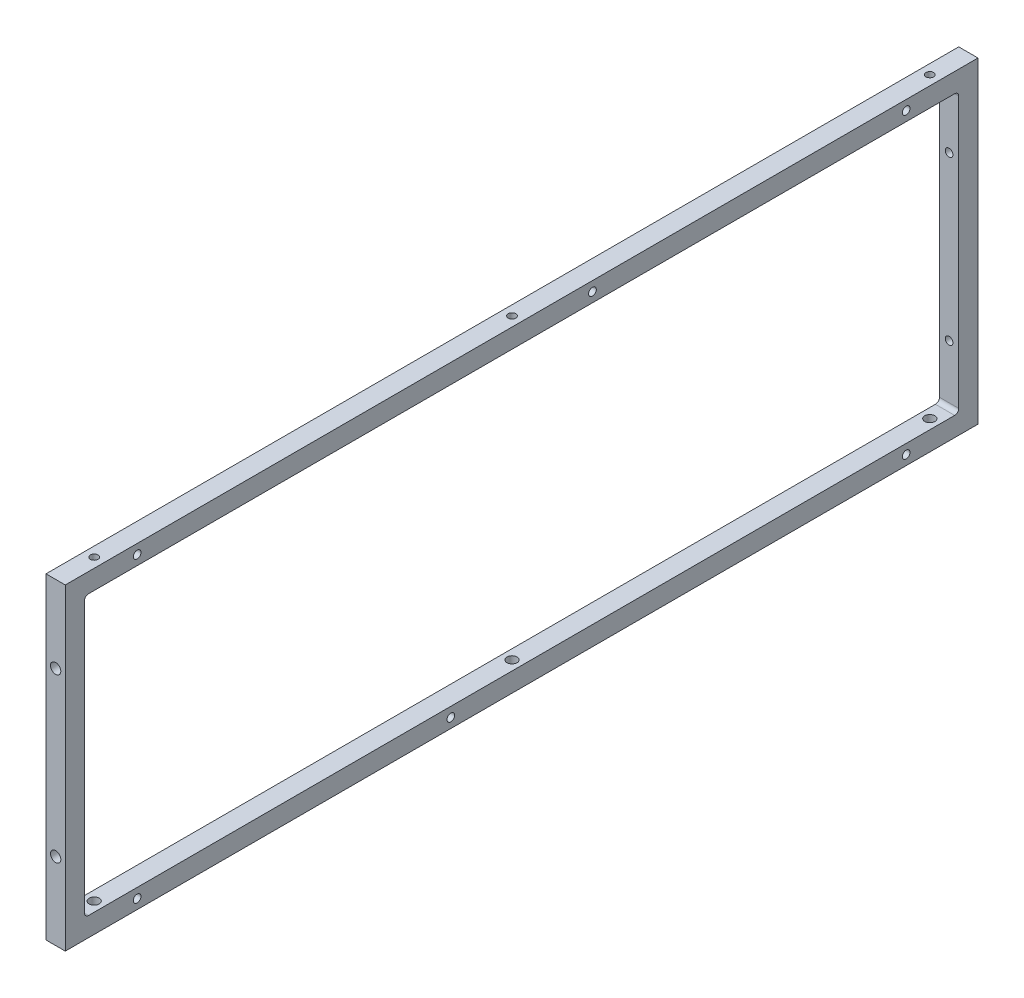
SolidWorks part; units mm, degrees
material "6061-T6 (SS)"
ref_plane "Front Plane" through (0, 0, 0) normal (0, 0, 1) x (1, 0, 0)
ref_plane "Top Plane" through (0, 0, 0) normal (0, 1, 0) x (1, 0, 0)
ref_plane "Right Plane" through (0, 0, 0) normal (1, 0, 0) x (0, 0, -1)
sketch "Sketch1" plane through (0, 0, 0) normal (1, 0, 0) x (0, 0, -1)
  line L0 (225.5, 78.3536) -> (-225.5, -78.3536) construction
  line L1 (-225.5, 78.3536) -> (225.5, 78.3536)
  line L2 (-225.5, 78.3536) -> (-225.5, -78.3536)
  line L3 (-225.5, -78.3536) -> (225.5, -78.3536)
  line L4 (225.5, 78.3536) -> (225.5, -78.3536)
  point P4 (0, 0)
  dimension "D1" = 451
  dimension "D2" = 156.7072
extrude "Extrude-Thin1" add sketch "Sketch1" along normal mid plane 9.525 thin
fillet "Fillet1" radius 2 4 edges at (0, -68.8286, -215.975) (0, -68.8286, 215.975) (0, 68.8286, 215.975) (0, 68.8286, -215.975)
hole_wizard "#10 Clearance Hole1" positions "Sketch3" profile "Sketch2" hole size "#10" standard "ANSI Inch"
sketch "Sketch3" plane through (0, -68.8286, 0) normal (0, 1, 0) x (1, 0, 0)
  line L0 (4.7625, -213.975) -> (4.7625, 213.975) construction
  line L1 (-4.7625, -213.975) -> (-4.7625, 213.975) construction
  line L3 (4.7625, 225.5) -> (-4.7625, 225.5) construction
  line L4 (4.7625, 225.5) -> (-4.7625, 225.5) construction
  line L5 (-4.7625, 0) -> (-100.6136, 0) construction
  line L6 (0, 206.45) -> (0, 397.3268) construction
  circle A0 centre (0, 206.45) radius 4.7625 construction
  point P0 (0, 206.45)
  point P2 (0, 0)
  point P26 (0, -206.45)
  dimension "D1" = 19.05
sketch "Sketch2" plane through (0, -68.8286, -206.45) normal (1, 0, 0) x (0, 0, 1)
  line L0 (0, 0) -> (0, 9.525)
  line L1 (0, 9.525) -> (2.4892, 9.525)
  line L2 (2.4892, 9.525) -> (2.4892, 0)
  line L5 (2.4892, 0) -> (0, 0)
  line L11 (0, -6.35) -> (0, 107.95) construction
  dimension "Thru Hole Dia." = 4.9784
  dimension "Thru Hole Depth" = 9.525
hole_wizard "#10-24 Tapped Hole1" positions "Sketch5" profile "Sketch4" tap size "#10-24" standard "ANSI Inch"
sketch "Sketch5" plane through (0, 0, -225.5) normal (0, 0, -1) x (-1, 0, 0)
  line L0 (0, 78.3536) -> (0, 173.2871) construction
  line L1 (-4.7625, 78.3536) -> (4.7625, 78.3536) construction
  line L2 (4.7625, 0) -> (23.2892, 0) construction
  line L3 (4.7625, -78.3536) -> (4.7625, 78.3536) construction
  point P0 (0, 40.2536)
  point P13 (0, -40.2536)
  dimension "D1" = 38.1
sketch "Sketch4" plane through (0, 40.2536, -225.5) normal (1, 0, 0) x (0, 1, 0)
  line L0 (0, 0) -> (0, 251.6008)
  line L1 (0, 251.6008) -> (1.8986, 250.46)
  line L2 (1.8986, 250.46) -> (1.8986, 0)
  line L5 (1.8986, 0) -> (0, 0)
  line L10 (0, 251.6008) -> (-1.8987, 250.46) construction
  line L11 (0, -6.35) -> (0, 107.95) construction
  dimension "Tap Drill Dia." = 3.7973
  dimension "Tap Drill Depth" = 250.46
  dimension "Drill Angle" = 118
cosmetic thread "Hole Thread1" parameters "D1"=9.525, "D2"=4.826
cosmetic thread "Hole Thread2" parameters "D1"=9.525, "D2"=4.826
hole_wizard "#10 Clearance Hole2" positions "Sketch7" profile "Sketch6" hole size "#10" standard "ANSI Inch"
sketch "Sketch7" plane through (0, 0, 225.5) normal (0, 0, 1) x (1, 0, 0)
  point P0 (0, 40.2536)
  point P3 (0, -40.2536)
sketch "Sketch6" plane through (0, 40.2536, 225.5) normal (1, 0, 0) x (0, -1, 0)
  line L0 (0, 0) -> (0, 21.5338)
  line L1 (0, 21.5338) -> (2.5527, 20)
  line L2 (2.5527, 20) -> (2.5527, 0)
  line L5 (2.5527, 0) -> (0, 0)
  line L10 (0, 21.5338) -> (-2.5527, 20) construction
  line L11 (0, -6.35) -> (0, 107.95) construction
  dimension "Hole Dia." = 5.1054
  dimension "Hole Depth" = 20
  dimension "Drill Angle" = 118
hole_wizard "#10-24 Tapped Hole2" positions "Sketch9" profile "Sketch8" tap size "#10-24" standard "ANSI Inch"
sketch "Sketch9" plane through (-4.7625, 0, 0) normal (-1, 0, 0) x (0, 0, 1)
  line L0 (0, 0) -> (0, 48.3235) construction
  line L1 (0, 0) -> (90.2804, 0) construction
  line L2 (-102.4491, 73.5911) -> (-75.598, 73.5911) construction
  line L3 (-225.5, 78.3536) -> (225.5, 78.3536) construction
  line L4 (-213.975, 68.8286) -> (213.975, 68.8286) construction
  line L5 (-151.0617, -73.5911) -> (-102.4491, -73.5911) construction
  circle A0 centre (-190, 73.5911) radius 4.7625 construction
  point P0 (-190, 73.5911)
  point P22 (-35, 73.5911)
  point P25 (-190, -73.5911)
  point P30 (35, -73.5911)
  point P33 (190, -73.5911)
  point P34 (190, 73.5911)
  dimension "D1" = 190
  dimension "D2" = 35
  dimension "D3" = 35
sketch "Sketch8" plane through (-4.7625, 73.5911, -190) normal (0, 1, 0) x (0, 0, 1)
  line L0 (0, 0) -> (0, 16.0908)
  line L1 (0, 16.0908) -> (1.8986, 14.95)
  line L2 (1.8986, 14.95) -> (1.8986, 0)
  line L5 (1.8986, 0) -> (0, 0)
  line L10 (0, 16.0908) -> (-1.8987, 14.95) construction
  line L11 (0, -6.35) -> (0, 107.95) construction
  dimension "Tap Drill Dia." = 3.7973
  dimension "Tap Drill Depth" = 14.95
  dimension "Drill Angle" = 118
cosmetic thread "Hole Thread4" parameters "D1"=9.525, "D2"=4.826
cosmetic thread "Hole Thread5" parameters "D1"=9.525, "D2"=4.826
cosmetic thread "Hole Thread6" parameters "D1"=9.525, "D2"=4.826
cosmetic thread "Hole Thread7" parameters "D1"=9.525, "D2"=4.826
cosmetic thread "Hole Thread8" parameters "D1"=9.525, "D2"=4.826
cosmetic thread "Hole Thread9" parameters "D1"=9.525, "D2"=4.826
hole_wizard "#10-24 Tapped Hole3" positions "Sketch11" profile "Sketch10" tap size "#10-24" standard "ANSI Inch"
sketch "Sketch11" plane through (0, 78.3536, 0) normal (0, 1, 0) x (1, 0, 0)
  point P0 (0, 206.45)
  point P3 (0, 0)
  point P6 (0, -206.45)
sketch "Sketch10" plane through (0, 78.3536, -206.45) normal (1, 0, 0) x (0, 0, 1)
  line L0 (0, 0) -> (0, 16.0908)
  line L1 (0, 16.0908) -> (1.8986, 14.95)
  line L2 (1.8986, 14.95) -> (1.8986, 0)
  line L5 (1.8986, 0) -> (0, 0)
  line L10 (0, 16.0908) -> (-1.8986, 14.95) construction
  line L11 (0, -6.35) -> (0, 107.95) construction
  dimension "Tap Drill Dia." = 3.7973
  dimension "Tap Drill Depth" = 14.95
  dimension "Drill Angle" = 118
cosmetic thread "Hole Thread10" parameters "D1"=9.525, "D2"=4.826
cosmetic thread "Hole Thread11" parameters "D1"=9.525, "D2"=4.826
cosmetic thread "Hole Thread12" parameters "D1"=9.525, "D2"=4.826
